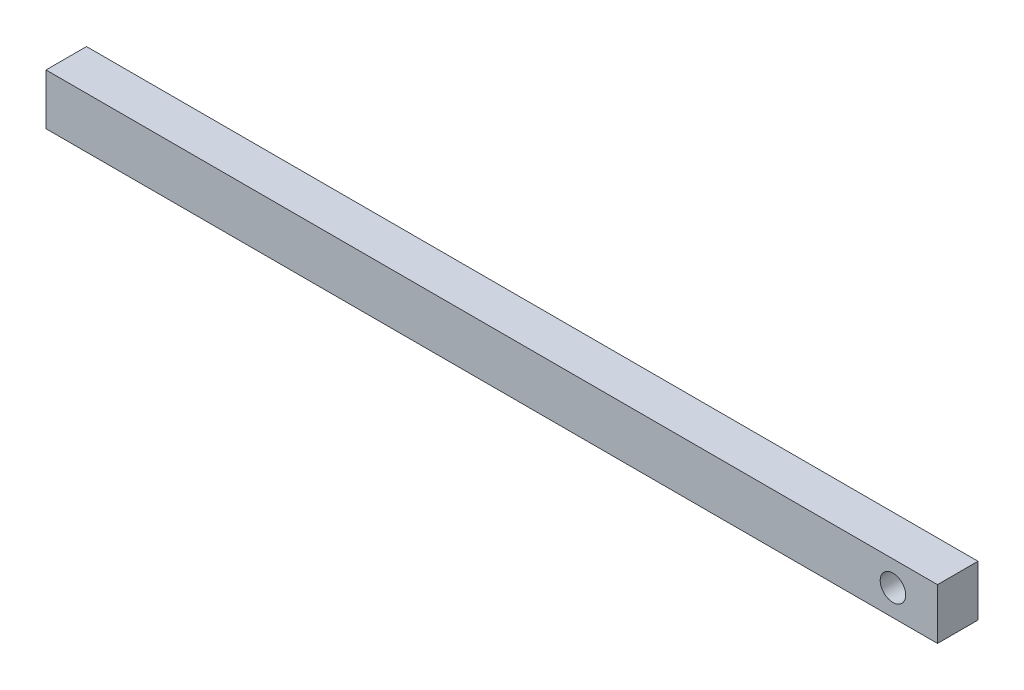
SolidWorks part; units mm, degrees
ref_plane "Front Plane" through (0, 0, 0) normal (0, 0, 1) x (1, 0, 0)
ref_plane "Top Plane" through (0, 0, 0) normal (0, 1, 0) x (1, 0, 0)
ref_plane "Right Plane" through (0, 0, 0) normal (1, 0, 0) x (0, 0, -1)
sketch "Sketch2" plane through (0, 0, 0) normal (0, 0, 1) x (1, 0, 0)
  line L1 (0, 0) -> (70, 0)
  line L2 (0, 0) -> (0, 4)
  line L3 (0, 4) -> (70, 4)
  line L4 (70, 0) -> (70, 4)
  dimension "D1" = 70
  dimension "D2" = 4
extrude "Boss-Extrude1" add sketch "Sketch2" along normal blind 3.18
sketch "Sketch4" plane through (0, 0, 3.18) normal (0, 0, 1) x (1, 0, 0)
  line L0 (70, 0) -> (70, 4) construction
  circle A0 centre (66.5002, 2.0348) radius 1
  point P4 (70, 2)
  dimension "D1" = 2
  dimension "D2" = 3.5
extrude "Cut-Extrude1" cut sketch "Sketch4" against normal blind 10
